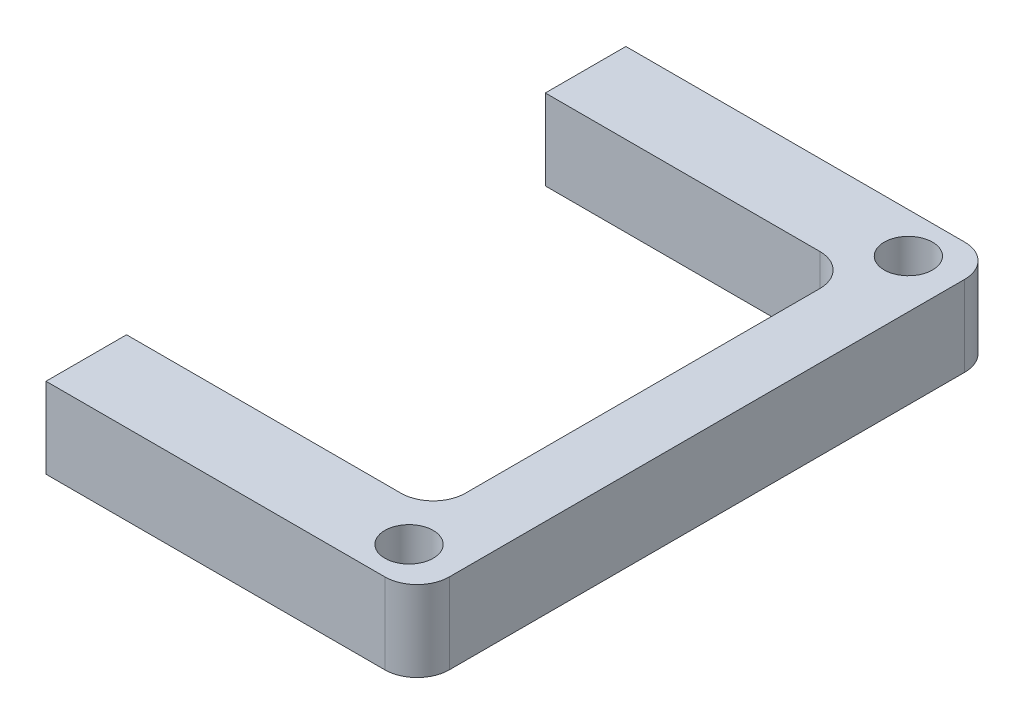
SolidWorks part; units mm, degrees
ref_plane "Front Plane" through (0, 0, 0) normal (0, 0, 1) x (1, 0, 0)
ref_plane "Top Plane" through (0, 0, 0) normal (0, 1, 0) x (1, 0, 0)
ref_plane "Right Plane" through (0, 0, 0) normal (1, 0, 0) x (0, 0, -1)
sketch "Sketch1" plane through (0, 0, 0) normal (0, 1, 0) x (1, 0, 0)
  line L0 (0, 5) -> (25, 5)
  line L1 (0, 0) -> (29, 0)
  line L2 (0, 0) -> (0, 5)
  line L3 (0, 36) -> (29, 36)
  line L4 (29, 0) -> (29, 36)
  line L5 (25, 5) -> (25, 31)
  line L6 (25, 31) -> (0, 31)
  line L7 (0, 0) -> (0, 5)
  line L8 (0, 31) -> (0, 36)
  line L9 (0, 31) -> (0, 36)
  circle A0 centre (3, 2.5) radius 1.5
  circle A1 centre (3, 33.5) radius 1.5
  circle A2 centre (26, 33.5) radius 1.5
  circle A3 centre (26, 2.5) radius 1.5
  dimension "D6" = 3
  dimension "D7" = 3
  dimension "D8" = 3
  dimension "D9" = 3
  dimension "D1" = 29
  dimension "D2" = 36
  dimension "D3" = 5
  dimension "D4" = 4
  dimension "D5" = 5
  dimension "D10" = 31
  dimension "D11" = 31
  dimension "D12" = 23
  dimension "D13" = 23
  dimension "D14" = 3
  dimension "D15" = 2.5
  dimension "D16" = 2.5
  dimension "D17" = 3
extrude "Boss-Extrude1" add sketch "Sketch1" along normal blind 5 contours L8 L6 L5 L0 L2 L1 L4 L3 A3 A2 A1 A0
sketch "Sketch2" plane through (0, 5, 0) normal (0, 1, 0) x (1, 0, 0)
  line L0 (0, 36) -> (29, 36) construction
  line L1 (-1.3155, 0) -> (5.9616, 0)
  line L2 (-1.3155, 0) -> (-1.3155, 36)
  line L3 (-1.3155, 36) -> (5.9616, 36)
  line L4 (5.9616, 0) -> (5.9616, 36)
fillet "Fillet1" radius 2 8 edges at (29, 2.5, -36) (29, 2.5, 0) (0, 2.5, 0) (0, 2.5, -5) (25, 2.5, -5) (25, 2.5, -31) (0, 2.5, -36) (0, 2.5, -31)
extrude "Cut-Extrude1" cut sketch "Sketch2" against normal blind 10
